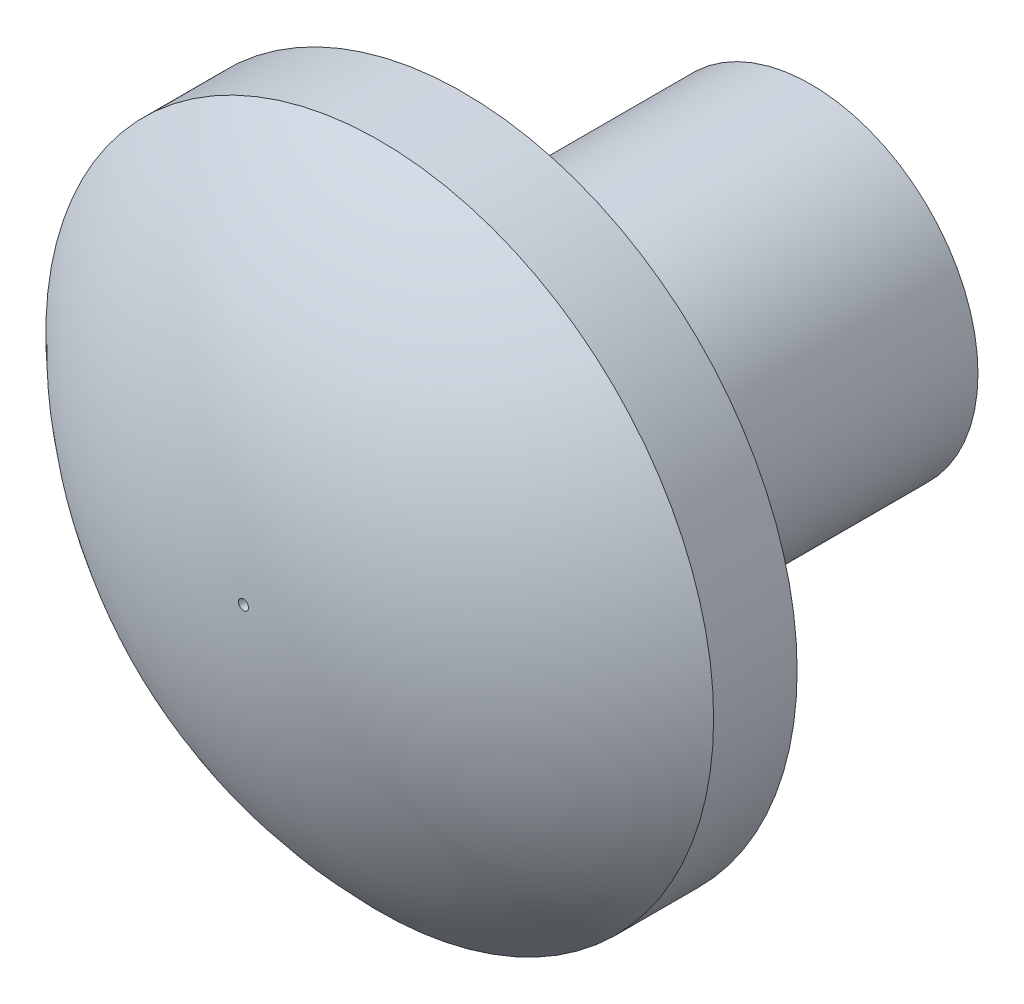
SolidWorks part; units mm, degrees
ref_plane "Front Plane" through (0, 0, 0) normal (0, 0, 1) x (1, 0, 0)
ref_plane "Top Plane" through (0, 0, 0) normal (0, 1, 0) x (1, 0, 0)
ref_plane "Right Plane" through (0, 0, 0) normal (1, 0, 0) x (0, 0, -1)
sketch "Sketch1" plane through (0, 0, 0) normal (0, 0, 1) x (1, 0, 0)
  circle A0 centre (0, 0) radius 3
  dimension "D1" = 6
extrude "Boss-Extrude1" add sketch "Sketch1" along normal blind 6.25
sketch "Sketch2" plane through (0, 0, 6.25) normal (0, 0, 1) x (1, 0, 0)
  circle A0 centre (0, 0) radius 6
  dimension "D1" = 12
extrude "Boss-Extrude2" add sketch "Sketch2" along normal blind 1.5 contours A0
sketch "Sketch3" plane through (0, 0, 0) normal (1, 0, 0) x (0, 0, -1)
  line L1 (-7.75, 6) -> (-7.75, 0.0904)
  line L3 (-10.1979, 0.0904) -> (-7.75, 0.0904)
  arc A0 (-7.75, 6) -> (-10.1979, 0.0904) centre (-1.8404, 0.0904) ccw
revolve "Revolve1" add sketch "Sketch3" angle 360 about axis through (0, 0, 6.25) along (0, 0, -1)
